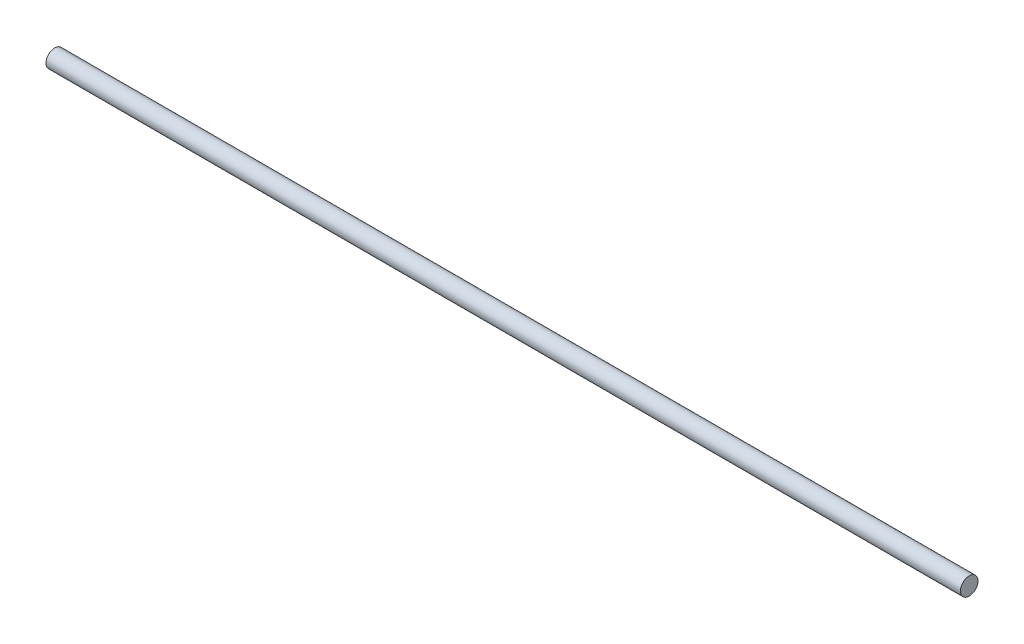
SolidWorks part; units mm, degrees
ref_plane "Front Plane" through (0, 0, 0) normal (0, 0, 1) x (1, 0, 0)
ref_plane "Top Plane" through (0, 0, 0) normal (0, 1, 0) x (1, 0, 0)
ref_plane "Right Plane" through (0, 0, 0) normal (1, 0, 0) x (0, 0, -1)
sketch "Sketch1" plane through (0, 0, 0) normal (1, 0, 0) x (0, 0, -1)
  circle A0 centre (0, 0) radius 6.35
  dimension "D1" = 12.7
extrude "Boss-Extrude1" add sketch "Sketch1" along normal mid plane 660.4
